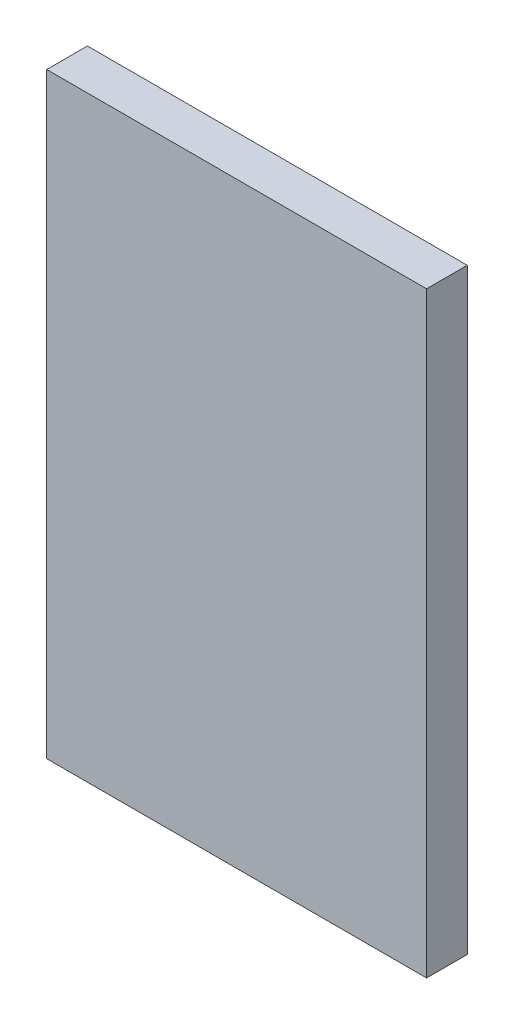
SolidWorks part; units mm, degrees
material "Oak"
ref_plane "Front Plane" through (0, 0, 0) normal (0, 0, 1) x (1, 0, 0)
ref_plane "Top Plane" through (0, 0, 0) normal (0, 1, 0) x (1, 0, 0)
ref_plane "Right Plane" through (0, 0, 0) normal (1, 0, 0) x (0, 0, -1)
sketch "Sketch1" plane through (0, 0, 0) normal (0, 0, 1) x (1, 0, 0)
  line L6 (-88.9, -139.7) -> (88.9, -139.7)
  line L8 (-88.9, -139.7) -> (-88.9, 139.7)
  line L9 (-88.9, 139.7) -> (88.9, 139.7)
  line L10 (88.9, -139.7) -> (88.9, 139.7)
  line L11 (-88.9, -139.7) -> (88.9, 139.7) construction
  line L12 (-88.9, 139.7) -> (88.9, -139.7) construction
  point P0 (0, 0)
  point P1 (0, 0)
  dimension "D1" = 279.4
  dimension "D2" = 177.8
extrude "Boss-Extrude1" add sketch "Sketch1" along normal blind 19.05
